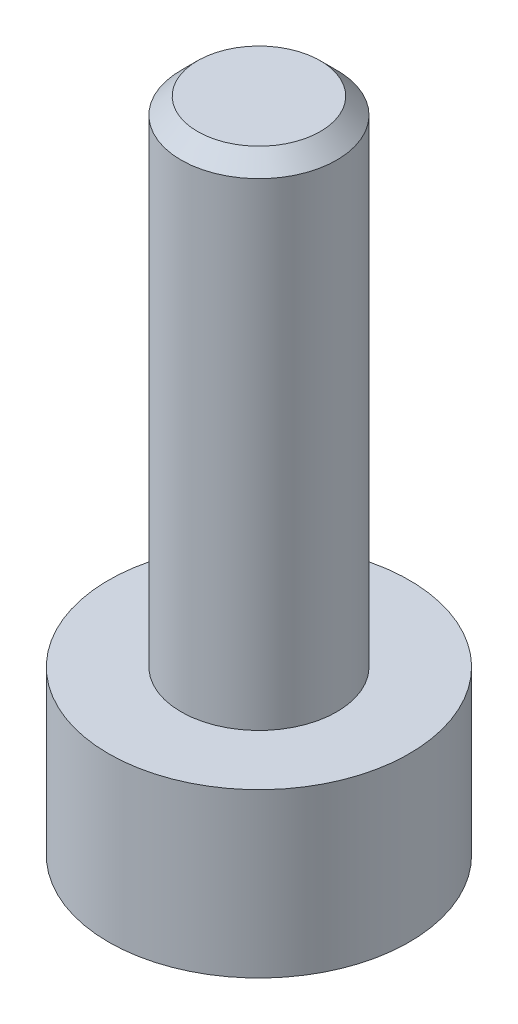
SolidWorks part; units mm, degrees
ref_plane "Front Plane" through (0, 0, 0) normal (0, 0, 1) x (1, 0, 0)
ref_plane "Top Plane" through (0, 0, 0) normal (0, 1, 0) x (1, 0, 0)
ref_plane "Right Plane" through (0, 0, 0) normal (1, 0, 0) x (0, 0, -1)
sketch "Sketch1" plane through (0, 0, 0) normal (0, 1, 0) x (1, 0, 0)
  circle A0 centre (0, 0) radius 1.825
  dimension "D1" = 3.65
extrude "Boss-Extrude1" add sketch "Sketch1" along normal blind 1.98
sketch "Sketch2" plane through (0, 1.98, 0) normal (0, 1, 0) x (1, 0, 0)
  circle A0 centre (0, 0) radius 0.945
  dimension "D1" = 1.89
extrude "Boss-Extrude2" add sketch "Sketch2" along normal blind 6
sketch "Sketch3" plane through (0, 0, 0) normal (0, -1, 0) x (1, 0, 0)
  line L1 (0.459, -0.795) -> (0.918, 0)
  line L2 (0.918, 0) -> (0.459, 0.795)
  line L3 (0.459, 0.795) -> (-0.459, 0.795)
  line L4 (-0.459, 0.795) -> (-0.918, 0)
  line L5 (-0.918, 0) -> (-0.459, -0.795)
  line L6 (-0.459, -0.795) -> (0.459, -0.795)
  circle A0 centre (0, 0) radius 0.795 construction
  dimension "D1" = 1.59
extrude "Cut-Extrude1" cut sketch "Sketch3" against normal blind 1
chamfer "Chamfer1" distance 0.2 angle 45 1 edges at (0, 7.98, 0.945)
